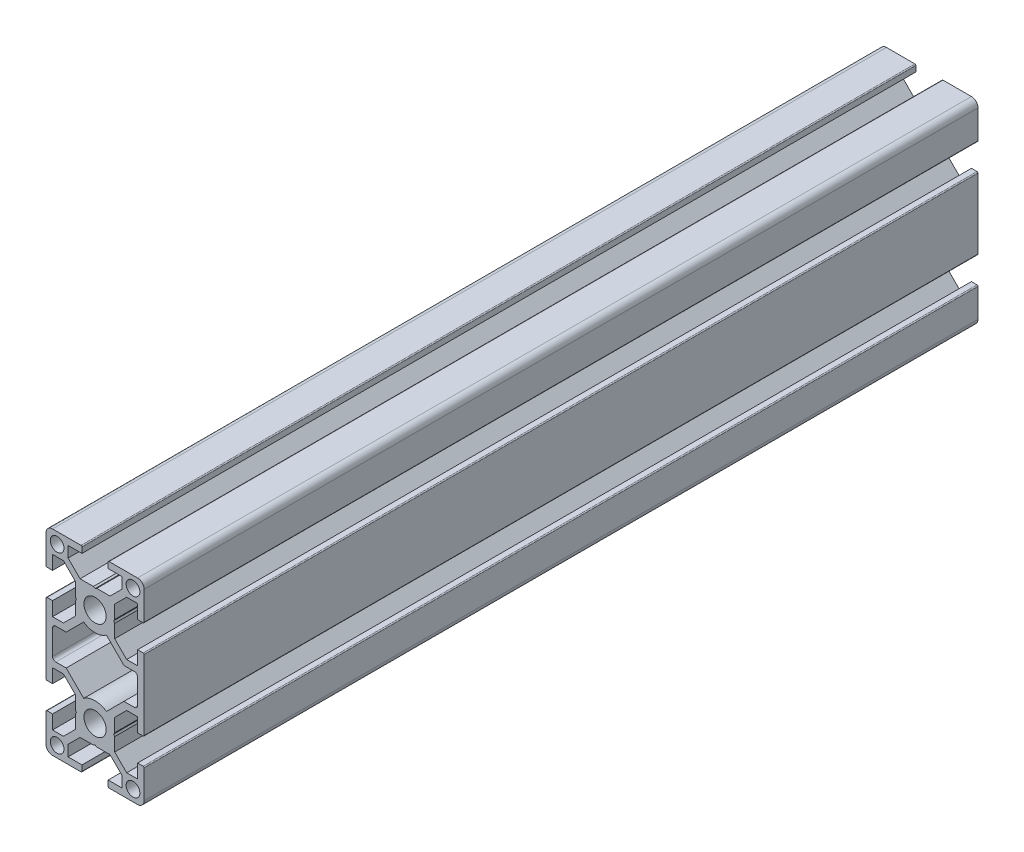
SolidWorks part; units mm, degrees
ref_plane "Front Plane" through (0, 0, 0) normal (0, 0, 1) x (1, 0, 0)
ref_plane "Top Plane" through (0, 0, 0) normal (0, 1, 0) x (1, 0, 0)
ref_plane "Right Plane" through (0, 0, 0) normal (1, 0, 0) x (0, 0, -1)
ref_plane "Plane1" through (0, 0, -1000) normal (0, 0, -1) x (-1, 0, 0)
sketch "Sketch1" plane through (0, 0, -1000) normal (0, 0, -1) x (-1, 0, 0)
  line L0 (13, 3.75) -> (13, -3.75)
  line L1 (12, -4.75) -> (8.8358, -4.75)
  line L2 (8.8358, -4.75) -> (3.4762, -10.1096)
  line L3 (-3.4762, -10.1096) -> (-8.8358, -4.75)
  line L4 (-8.8358, -4.75) -> (-12, -4.75)
  line L5 (-13, -3.75) -> (-13, 3.75)
  line L6 (-12, 4.75) -> (-8.8358, 4.75)
  line L7 (-8.8358, 4.75) -> (-3.4762, 10.1096)
  line L8 (3.4762, 10.1096) -> (8.8358, 4.75)
  line L9 (8.8358, 4.75) -> (12, 4.75)
  line L10 (15, -28) -> (15, -19.3)
  line L11 (14.7, -19) -> (13, -19)
  line L12 (13, -19) -> (13, -23.25)
  line L13 (13, -23.25) -> (9.6642, -23.25)
  line L14 (9.6642, -23.25) -> (6, -19.5858)
  line L15 (6, -19.5858) -> (6, -15.5196)
  line L16 (6, -15.5196) -> (5.7, -15)
  line L17 (5.7, -15) -> (6, -14.4804)
  line L18 (6, -14.4804) -> (6, -10.4142)
  line L19 (6, -10.4142) -> (9.6642, -6.75)
  line L20 (9.6642, -6.75) -> (13, -6.75)
  line L21 (13, -6.75) -> (13, -11)
  line L22 (13, -11) -> (14.7, -11)
  line L23 (15, -10.7) -> (15, 10.7)
  line L24 (14.7, 11) -> (13, 11)
  line L25 (13, 11) -> (13, 6.75)
  line L26 (13, 6.75) -> (9.6642, 6.75)
  line L27 (9.6642, 6.75) -> (6, 10.4142)
  line L28 (6, 10.4142) -> (6, 14.4804)
  line L29 (6, 14.4804) -> (5.7, 15)
  line L30 (5.7, 15) -> (6, 15.5196)
  line L31 (6, 15.5196) -> (6, 19.5858)
  line L32 (6, 19.5858) -> (9.6642, 23.25)
  line L33 (9.6642, 23.25) -> (13, 23.25)
  line L34 (13, 23.25) -> (13, 19)
  line L35 (13, 19) -> (14.7, 19)
  line L36 (15, 19.3) -> (15, 28)
  line L37 (13, 30) -> (4.3, 30)
  line L38 (4, 29.7) -> (4, 28)
  line L39 (4, 28) -> (8.25, 28)
  line L40 (8.25, 28) -> (8.25, 24.6642)
  line L41 (8.25, 24.6642) -> (4.5858, 21)
  line L42 (4.5858, 21) -> (0.5196, 21)
  line L43 (0.5196, 21) -> (0, 20.7)
  line L44 (0, 20.7) -> (-0.5196, 21)
  line L45 (-0.5196, 21) -> (-4.5858, 21)
  line L46 (-4.5858, 21) -> (-8.25, 24.6642)
  line L47 (-8.25, 24.6642) -> (-8.25, 28)
  line L48 (-8.25, 28) -> (-4, 28)
  line L49 (-4, 28) -> (-4, 29.7)
  line L50 (-4.3, 30) -> (-13, 30)
  line L51 (-15, 28) -> (-15, 19.3)
  line L52 (-14.7, 19) -> (-13, 19)
  line L53 (-13, 19) -> (-13, 23.25)
  line L54 (-13, 23.25) -> (-9.6642, 23.25)
  line L55 (-9.6642, 23.25) -> (-6, 19.5858)
  line L56 (-6, 19.5858) -> (-6, 15.5196)
  line L57 (-6, 15.5196) -> (-5.7, 15)
  line L58 (-5.7, 15) -> (-6, 14.4804)
  line L59 (-6, 14.4804) -> (-6, 10.4142)
  line L60 (-6, 10.4142) -> (-9.6642, 6.75)
  line L61 (-9.6642, 6.75) -> (-13, 6.75)
  line L62 (-13, 6.75) -> (-13, 11)
  line L63 (-13, 11) -> (-14.7, 11)
  line L64 (-15, 10.7) -> (-15, -10.7)
  line L65 (-14.7, -11) -> (-13, -11)
  line L66 (-13, -11) -> (-13, -6.75)
  line L67 (-13, -6.75) -> (-9.6642, -6.75)
  line L68 (-9.6642, -6.75) -> (-6, -10.4142)
  line L69 (-6, -10.4142) -> (-6, -14.4804)
  line L70 (-6, -14.4804) -> (-5.7, -15)
  line L71 (-5.7, -15) -> (-6, -15.5196)
  line L72 (-6, -15.5196) -> (-6, -19.5858)
  line L73 (-6, -19.5858) -> (-9.6642, -23.25)
  line L74 (-9.6642, -23.25) -> (-13, -23.25)
  line L75 (-13, -23.25) -> (-13, -19)
  line L76 (-13, -19) -> (-14.7, -19)
  line L77 (-15, -19.3) -> (-15, -28)
  line L78 (-13, -30) -> (-4.3, -30)
  line L79 (-4, -29.7) -> (-4, -28)
  line L80 (-4, -28) -> (-8.25, -28)
  line L81 (-8.25, -28) -> (-8.25, -24.6642)
  line L82 (-8.25, -24.6642) -> (-4.5858, -21)
  line L83 (-4.5858, -21) -> (-0.5196, -21)
  line L84 (-0.5196, -21) -> (0, -20.7)
  line L85 (0, -20.7) -> (0.5196, -21)
  line L86 (0.5196, -21) -> (4.5858, -21)
  line L87 (4.5858, -21) -> (8.25, -24.6642)
  line L88 (8.25, -24.6642) -> (8.25, -28)
  line L89 (8.25, -28) -> (4, -28)
  line L90 (4, -28) -> (4, -29.7)
  line L91 (4.3, -30) -> (13, -30)
  circle A0 centre (11.6, 26.625) radius 2.1
  circle A1 centre (11.6, -26.625) radius 2.1
  arc A2 (12, 4.75) -> (13, 3.75) centre (12, 3.75) cw
  arc A3 (13, -3.75) -> (12, -4.75) centre (12, -3.75) cw
  arc A4 (3.4762, -10.1096) -> (-3.4762, -10.1096) centre (0, -15) ccw
  arc A5 (-12, -4.75) -> (-13, -3.75) centre (-12, -3.75) cw
  arc A6 (-13, 3.75) -> (-12, 4.75) centre (-12, 3.75) cw
  arc A7 (-3.4762, 10.1096) -> (3.4762, 10.1096) centre (0, 15) ccw
  circle A8 centre (0, -15) radius 3.4
  circle A9 centre (0, 15) radius 3.4
  circle A10 centre (-11.6, 26.625) radius 2.1
  circle A11 centre (-11.6, -26.625) radius 2.1
  arc A12 (15, -19.3) -> (14.7, -19) centre (14.7, -19.3) ccw
  arc A13 (14.7, -11) -> (15, -10.7) centre (14.7, -10.7) ccw
  arc A14 (15, 10.7) -> (14.7, 11) centre (14.7, 10.7) ccw
  arc A15 (14.7, 19) -> (15, 19.3) centre (14.7, 19.3) ccw
  arc A16 (15, 28) -> (13, 30) centre (13, 28) ccw
  arc A17 (4.3, 30) -> (4, 29.7) centre (4.3, 29.7) ccw
  arc A18 (-4, 29.7) -> (-4.3, 30) centre (-4.3, 29.7) ccw
  arc A19 (-13, 30) -> (-15, 28) centre (-13, 28) ccw
  arc A20 (-15, 19.3) -> (-14.7, 19) centre (-14.7, 19.3) ccw
  arc A21 (-14.7, 11) -> (-15, 10.7) centre (-14.7, 10.7) ccw
  arc A22 (-15, -10.7) -> (-14.7, -11) centre (-14.7, -10.7) ccw
  arc A23 (-14.7, -19) -> (-15, -19.3) centre (-14.7, -19.3) ccw
  arc A24 (-15, -28) -> (-13, -30) centre (-13, -28) ccw
  arc A25 (-4.3, -30) -> (-4, -29.7) centre (-4.3, -29.7) ccw
  arc A26 (4, -29.7) -> (4.3, -30) centre (4.3, -29.7) ccw
  arc A27 (13, -30) -> (15, -28) centre (13, -28) ccw
extrude "Boss-Extrude1" add sketch "Sketch1" against normal blind 255
